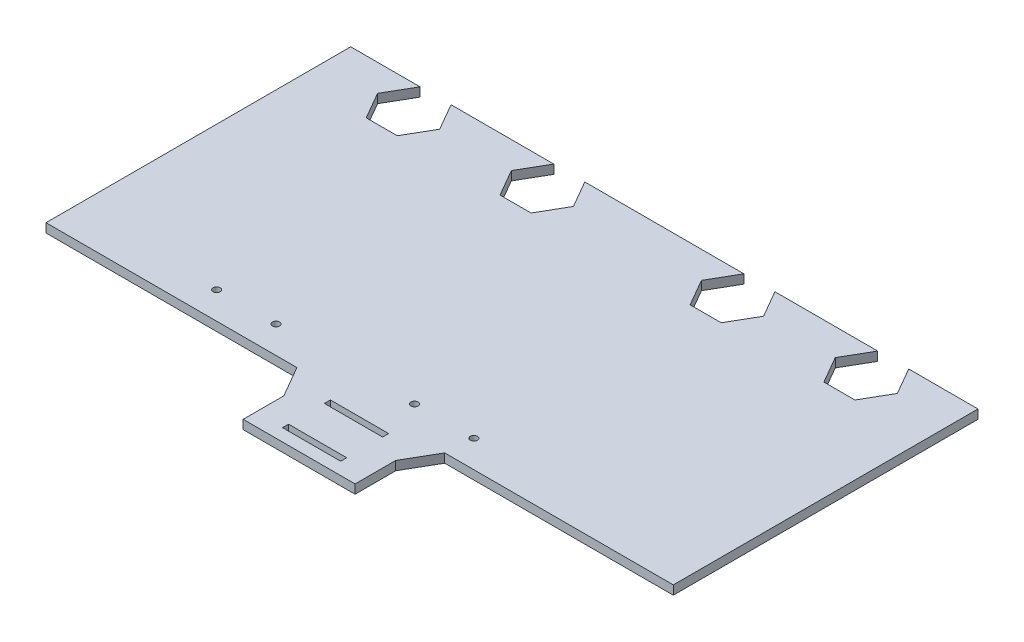
SolidWorks part; units mm, degrees
ref_plane "Front Plane" through (0, 0, 0) normal (0, 0, 1) x (1, 0, 0)
ref_plane "Top Plane" through (0, 0, 0) normal (0, 1, 0) x (1, 0, 0)
ref_plane "Right Plane" through (0, 0, 0) normal (1, 0, 0) x (0, 0, -1)
sketch "Sketch1" plane through (0, 0, 0) normal (0, 1, 0) x (1, 0, 0)
  line L1 (0, 0) -> (444.5, 0)
  line L2 (0, 0) -> (0, 215.9)
  line L3 (0, 215.9) -> (444.5, 215.9)
  line L4 (444.5, 0) -> (444.5, 215.9)
  line L5 (0, 0) -> (444.5, 215.9) construction
  line L6 (0, 215.9) -> (444.5, 0) construction
  point P4 (222.25, 107.95)
  dimension "D1" = 444.5
  dimension "D2" = 215.9
extrude "Boss-Extrude1" add sketch "Sketch1" along normal blind 6.35
sketch "Sketch2" plane through (0, 0, 0) normal (0, -1, 0) x (1, 0, 0)
  line L0 (0, 0) -> (444.5, 0) construction
  line L1 (269.8, 0) -> (190.5, 0)
  line L2 (269.8, 0) -> (269.8, 50.8)
  line L3 (269.8, 50.8) -> (190.5, 50.8)
  line L4 (190.5, 0) -> (190.5, 50.8)
  line L5 (269.8, 0) -> (190.5, 50.8) construction
  line L6 (269.8, 50.8) -> (190.5, 0) construction
  line L7 (230.15, -215.9) -> (230.15, 0) construction
  line L10 (444.5, -215.9) -> (0, -215.9) construction
  point P4 (230.15, 25.4)
  dimension "D1" = 79.3
  dimension "D2" = 50.8
  dimension "D3" = 190.5
extrude "Boss-Extrude2" add sketch "Sketch2" against normal up to surface (6.35 mm away) up to face at (222.25, 6.35, -107.95)
sketch "Sketch3" plane through (0, 6.35, 0) normal (0, 1, 0) x (1, 0, 0)
  line L1 (209.55, -8) -> (250.8, -8)
  line L2 (209.55, -8) -> (209.55, -12.28)
  line L3 (209.55, -12.28) -> (250.8, -12.28)
  line L4 (250.8, -8) -> (250.8, -12.28)
  line L5 (209.55, -8) -> (250.8, -12.28) construction
  line L6 (209.55, -12.28) -> (250.8, -8) construction
  line L7 (209.55, -37.7) -> (250.8, -37.7)
  line L8 (209.55, -37.7) -> (209.55, -41.98)
  line L9 (209.55, -41.98) -> (250.8, -41.98)
  line L10 (250.8, -37.7) -> (250.8, -41.98)
  line L11 (209.55, -37.7) -> (250.8, -41.98) construction
  line L12 (209.55, -41.98) -> (250.8, -37.7) construction
  line L13 (269.8, -50.8) -> (269.8, 0) construction
  line L14 (269.8, 0) -> (444.5, 0) construction
  line L15 (190.5, 0) -> (190.5, -50.8) construction
  point P4 (230.175, -10.14)
  point P9 (230.175, -39.84)
  dimension "D1" = 4.28
  dimension "D2" = 19.05
  dimension "D3" = 25.42
  dimension "D4" = 19
  dimension "D5" = 8
extrude "Cut-Extrude1" cut sketch "Sketch3" against normal through all
sketch "Sketch4" plane through (0, 6.35, 0) normal (0, 1, 0) x (1, 0, 0)
  line L7 (190.5, -21.997) -> (177.8, 0)
  line L8 (190.5, 0) -> (190.5, -50.8) construction
  line L9 (0, 0) -> (190.5, 0) construction
  line L10 (177.8, 0) -> (190.5, 0)
  line L11 (190.5, 0) -> (190.5, -21.997)
  line L12 (269.8, 0) -> (269.8, -21.997)
  line L13 (269.8, -50.8) -> (269.8, 0) construction
  line L14 (269.8, -21.997) -> (282.5, 0)
  line L15 (269.8, 0) -> (444.5, 0) construction
  line L16 (282.5, 0) -> (269.8, 0)
  dimension "D1" = 25.4
  dimension "D2" = 12.7
extrude "Boss-Extrude3" add sketch "Sketch4" against normal up to surface (6.35 mm away) up to face at (230.175, 0, 10.14)
sketch "Sketch5" plane through (0, 6.35, 0) normal (0, 1, 0) x (1, 0, 0)
  line L0 (444.5, 215.9) -> (0, 215.9) construction
  line L1 (406.4, 196.85) -> (395.4015, 215.9)
  line L2 (395.4015, 215.9) -> (373.4044, 215.9)
  line L3 (373.4044, 215.9) -> (362.4059, 196.85)
  line L4 (362.4059, 196.85) -> (373.4044, 177.8)
  line L5 (373.4044, 177.8) -> (395.4015, 177.8)
  line L6 (395.4015, 177.8) -> (406.4, 196.85)
  line L7 (444.5, 0) -> (444.5, 215.9) construction
  line L8 (337.0059, 215.9) -> (337.0059, 320.0612) construction
  line L10 (278.6103, 177.8) -> (267.6118, 196.85)
  line L11 (300.6074, 177.8) -> (278.6103, 177.8)
  line L12 (311.6059, 196.85) -> (300.6074, 177.8)
  line L13 (300.6074, 215.9) -> (311.6059, 196.85)
  line L14 (278.6103, 215.9) -> (300.6074, 215.9)
  line L15 (267.6118, 196.85) -> (278.6103, 215.9)
  line L16 (222.25, 215.9) -> (222.25, -50.8) construction
  line L17 (444.5, 215.9) -> (0, 215.9) construction
  line L18 (190.5, -50.8) -> (269.8, -50.8) construction
  line L19 (176.8882, 196.85) -> (165.8897, 215.9)
  line L20 (165.8897, 215.9) -> (143.8926, 215.9)
  line L21 (143.8926, 215.9) -> (132.8941, 196.85)
  line L22 (132.8941, 196.85) -> (143.8926, 177.8)
  line L23 (143.8926, 177.8) -> (165.8897, 177.8)
  line L24 (165.8897, 177.8) -> (176.8882, 196.85)
  line L25 (49.0985, 177.8) -> (38.1, 196.85)
  line L26 (71.0956, 177.8) -> (49.0985, 177.8)
  line L27 (82.0941, 196.85) -> (71.0956, 177.8)
  line L28 (71.0956, 215.9) -> (82.0941, 196.85)
  line L29 (49.0985, 215.9) -> (71.0956, 215.9)
  line L30 (38.1, 196.85) -> (49.0985, 215.9)
  circle A0 centre (384.403, 196.85) radius 19.05 construction
  circle A1 centre (289.6089, 196.85) radius 19.05 construction
  circle A2 centre (154.8911, 196.85) radius 19.05 construction
  circle A3 centre (60.097, 196.85) radius 19.05 construction
  dimension "D1" = 38.1
  dimension "D2" = 19.05
  dimension "D3" = 25.4
extrude "Cut-Extrude2" cut sketch "Sketch5" against normal through all
sketch "Sketch6" plane through (0, 6.35, 0) normal (0, 1, 0) x (1, 0, 0)
  line L0 (0, 19.3) -> (444.5, 19.3) construction
  line L1 (0, 215.9) -> (0, 0) construction
  line L2 (444.5, 0) -> (444.5, 215.9) construction
  line L3 (0, 0) -> (177.8, 0) construction
  circle A0 centre (101.6, 19.3) radius 2.5
  circle A1 centre (143.66, 19.3) radius 2.5
  circle A2 centre (241.84, 19.3) radius 2.5
  circle A3 centre (283.9, 19.3) radius 2.5
  dimension "D2" = 5
  dimension "D1" = 19.3
  dimension "D3" = 101.6
  dimension "D4" = 42.06
  dimension "D5" = 42.06
  dimension "D6" = 98.18
extrude "Cut-Extrude3" cut sketch "Sketch6" against normal through all
